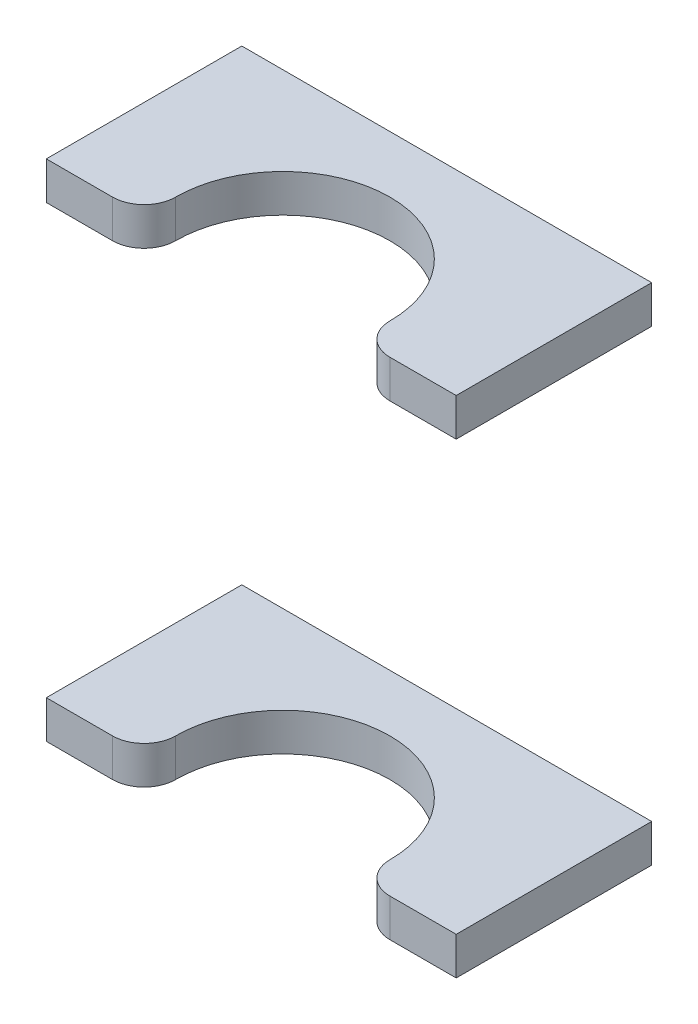
SolidWorks part; units mm, degrees
material "1.0553 (S355J0)"
ref_plane "Front Plane" through (0, 0, 0) normal (0, 0, 1) x (1, 0, 0)
ref_plane "Top Plane" through (0, 0, 0) normal (0, 1, 0) x (1, 0, 0)
ref_plane "Right Plane" through (0, 0, 0) normal (1, 0, 0) x (0, 0, -1)
sketch "Sketch1" plane through (0, 0, 0) normal (0, 0, 1) x (1, 0, 0)
  line L0 (-347.5, 0) -> (-347.5, 120) construction
  line L1 (660, 0) -> (-660, 0) construction
  line L2 (-660, 120) -> (660, 120) construction
  line L3 (-347.5, 60) -> (-213.0727, 60) construction
  line L4 (-315, 20) -> (-380, 20)
  line L5 (-315, 20) -> (-315, 26)
  line L6 (-315, 26) -> (-380, 26)
  line L7 (-380, 20) -> (-380, 26)
  line L8 (-315, 20) -> (-380, 26) construction
  line L9 (-315, 26) -> (-380, 20) construction
  line L10 (-315, 94) -> (-380, 100) construction
  line L11 (-315, 100) -> (-380, 94) construction
  line L12 (-380, 100) -> (-380, 94)
  line L13 (-315, 94) -> (-380, 94)
  line L14 (-315, 100) -> (-315, 94)
  line L15 (-315, 100) -> (-380, 100)
  line L16 (-420, 160.1311) -> (-420, -299.8689) construction
  point P6 (-347.5, 23)
  point P17 (-347.5, 97)
  dimension "D1" = 6
  dimension "D2" = 65
  dimension "D3" = 20
  dimension "D4" = 40
extrude "Boss-Extrude1" add sketch "Sketch1" along normal up to surface (46 mm away)
sketch "Sketch4" plane through (0, 20, 0) normal (0, -1, 0) x (-1, 0, 0)
  line L0 (420, -26) -> (315, -26) construction
  line L1 (420, -46) -> (420, -6) construction
  line L2 (315, -46) -> (315, 0) construction
  line L3 (347.5, -46) -> (347.5, -26) construction
  line L4 (380, -46) -> (315, -46) construction
  line L5 (315, -31) -> (315, -46)
  line L6 (380, -31) -> (380, -46)
  line L7 (380, -46) -> (315, -46)
  line L9 (369.5, -31) -> (380, -31)
  line L12 (325.5, -31) -> (315, -31)
  arc A0 (364.5, -26) -> (330.5, -26) centre (347.5, -26) ccw
  arc A1 (364.5, -26) -> (369.5, -31) centre (369.5, -26) ccw
  arc A2 (330.5, -26) -> (325.5, -31) centre (325.5, -26) cw
  dimension "D1" = 34
  dimension "D2" = 5
extrude "Cut-Extrude4" cut sketch "Sketch4" against normal through all
